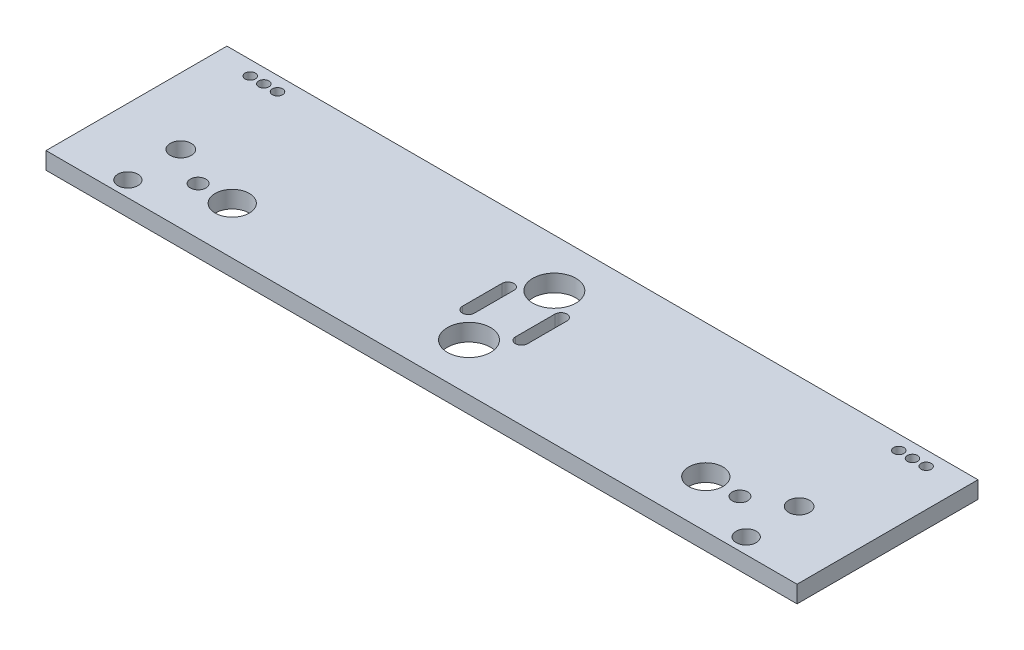
SolidWorks part; units mm, degrees
ref_plane "Front Plane" through (0, 0, 0) normal (0, 0, 1) x (1, 0, 0)
ref_plane "Top Plane" through (0, 0, 0) normal (0, 1, 0) x (1, 0, 0)
ref_plane "Right Plane" through (0, 0, 0) normal (1, 0, 0) x (0, 0, -1)
sketch "Sketch1" plane through (0, 0, 0) normal (0, 1, 0) x (1, 0, 0)
  line L0 (-52.3944, 23.1612) -> (-52.3944, 11.5912)
  line L1 (-152.8644, 43.087) -> (67.1356, 43.087)
  line L2 (-152.8644, 43.087) -> (-152.8644, -9.913)
  line L3 (-152.8644, -9.913) -> (67.1356, -9.913)
  line L4 (67.1356, 43.087) -> (67.1356, -9.913)
  line L5 (-48.8744, 23.1612) -> (-48.8744, 11.5912)
  line L6 (-36.8544, 23.1612) -> (-36.8544, 11.5912)
  line L7 (-33.3344, 11.5912) -> (-33.3344, 23.1612)
  circle A0 centre (56.1356, 38.907) radius 1.505
  circle A1 centre (52.1256, 38.907) radius 1.505
  circle A2 centre (48.1156, 38.907) radius 1.505
  circle A3 centre (-141.8744, 38.907) radius 1.505
  circle A4 centre (-137.8744, 38.907) radius 1.505
  circle A5 centre (-133.8744, 38.907) radius 1.505
  circle A6 centre (-42.8644, 28.998) radius 6.315
  circle A7 centre (-42.8644, 3.998) radius 6.315
  arc A8 (-52.3944, 23.1612) -> (-48.8744, 23.1612) centre (-50.6344, 23.1612) cw
  arc A9 (-48.8744, 11.5912) -> (-52.3944, 11.5912) centre (-50.6344, 11.5912) cw
  arc A10 (-36.8544, 11.5912) -> (-33.3344, 11.5912) centre (-35.0944, 11.5912) ccw
  arc A11 (-33.3344, 23.1612) -> (-36.8544, 23.1612) centre (-35.0944, 23.1612) ccw
  circle A12 centre (47.6973, 10.1273) radius 3.0784
  circle A13 centre (47.6973, -5.3727) radius 2.9298
  circle A14 centre (36.4973, 3.998) radius 2.275
  circle A15 centre (26.4973, 3.998) radius 5
  circle A16 centre (-133.4261, -5.3727) radius 2.9298
  circle A17 centre (-133.4261, 10.1273) radius 3.0784
  circle A18 centre (-122.2261, 3.998) radius 2.275
  circle A19 centre (-112.2261, 3.998) radius 5
  point P0 (-42.8644, 16.587)
  dimension "D3" = 4.01
  dimension "D7" = 4
  dimension "D16" = 12.63
  dimension "D17" = 12.63
  dimension "D18" = 15.5
  dimension "D25" = 4.55
  dimension "D26" = 10
  dimension "D1" = 220
  dimension "D2" = 53
  dimension "D4" = 4.01
  dimension "D5" = 11
  dimension "D6" = 4
  dimension "D8" = 10.99
  dimension "D27" = 11.2
  dimension "D28" = 10
extrude "Boss-Extrude1" add sketch "Sketch1" along normal blind 5
